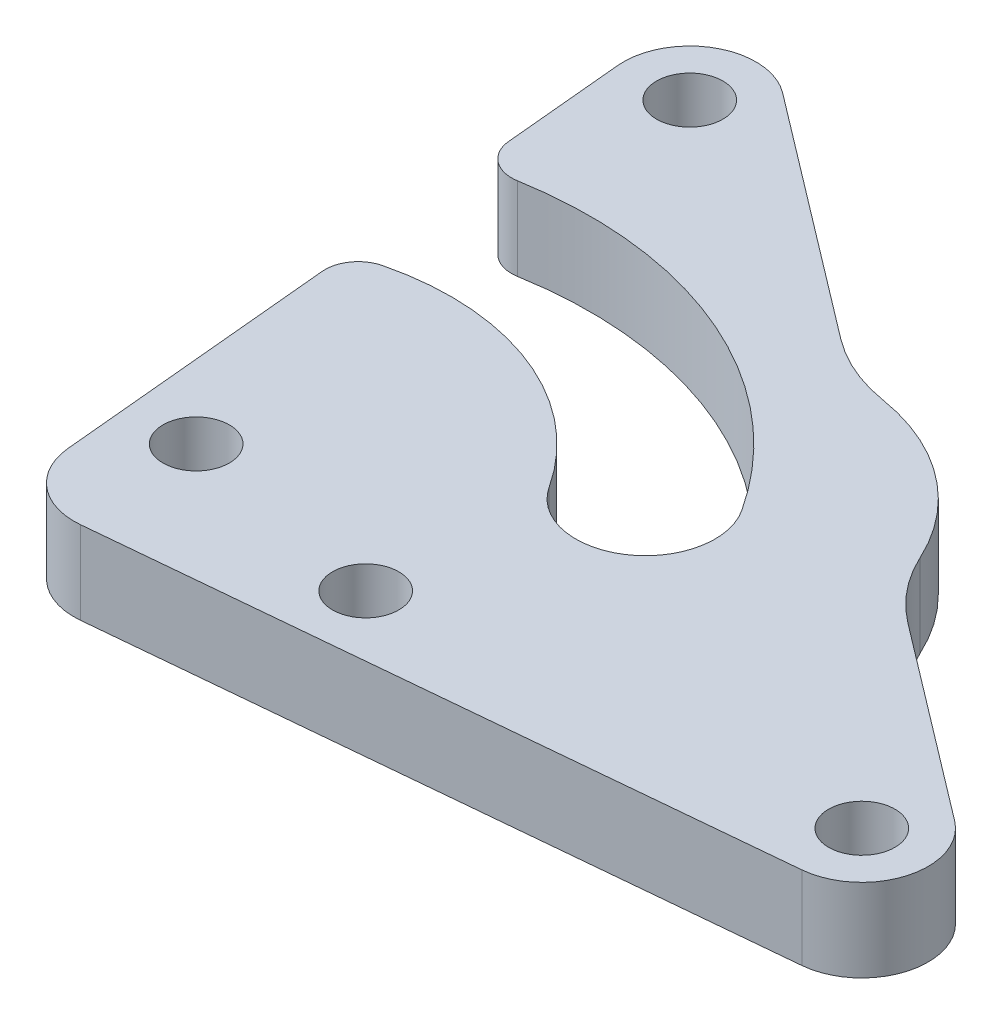
SolidWorks part; units mm, degrees
ref_plane "前视基准面" through (0, 0, 0) normal (0, 0, 1) x (1, 0, 0)
ref_plane "上视基准面" through (0, 0, 0) normal (0, 1, 0) x (1, 0, 0)
ref_plane "右视基准面" through (0, 0, 0) normal (1, 0, 0) x (0, 0, -1)
sketch "草图1" plane through (0, 0, 0) normal (0, 1, 0) x (1, 0, 0)
  line L0 (-20.0875, 0) -> (20.0875, 0) construction
  line L1 (-20.0875, 0) -> (-23.165, 32.8682) construction
  line L2 (-20.0875, 0) -> (-23.165, 32.8682) construction
  line L3 (-23.165, 32.8682) -> (20.0875, 0) construction
  line L4 (-20.0875, 0) -> (-23.165, 32.8682) construction
  line L5 (-24.0701, -0.3729) -> (-27.1475, 32.4954)
  line L6 (-16.1049, 0.3729) -> (-19.1824, 33.2411)
  line L7 (-23.165, 32.8682) -> (20.0875, 0) construction
  line L8 (-20.7448, 36.053) -> (22.5077, 3.1848)
  line L9 (-25.5851, 29.6835) -> (17.6673, -3.1848)
  line L10 (-20.0875, 0) -> (20.0875, 0) construction
  line L11 (-20.0875, 4) -> (20.0875, 4)
  line L12 (-20.0875, -4) -> (20.0875, -4)
  arc A0 (-24.0701, -0.3729) -> (-16.1049, 0.3729) centre (-20.0875, 0) ccw
  arc A1 (-19.1824, 33.2411) -> (-27.1475, 32.4954) centre (-23.165, 32.8682) ccw
  arc A2 (-20.7448, 36.053) -> (-25.5851, 29.6835) centre (-23.165, 32.8682) ccw
  arc A3 (17.6673, -3.1848) -> (22.5077, 3.1848) centre (20.0875, 0) ccw
  arc A4 (-20.0875, 4) -> (-20.0875, -4) centre (-20.0875, 0) ccw
  arc A5 (20.0875, -4) -> (20.0875, 4) centre (20.0875, 0) ccw
  circle A6 centre (-20.0875, 0) radius 2
  circle A7 centre (-23.165, 32.8682) radius 2
  circle A8 centre (20.0875, 0) radius 2
  point P4 (0, 0)
  point P7 (-21.6262, 16.4341)
  point P12 (-1.5387, 16.4341)
  point P18 (0, 0)
  dimension "D4" = 4
  dimension "D5" = 4
  dimension "D6" = 4
  dimension "D7" = 4
  dimension "D8" = 4
  dimension "D1" = 40.175
  dimension "D2" = 33.012
  dimension "D3" = 54.324
extrude "凸台-拉伸1" add sketch "草图1" along normal blind 5 contours L11 A4 A0 L6 A6 | A4 L11 L6 L9 A2 L5 | A1 A2 L9 L6 A7 | A5 L8 A1 L6 L9 L11 | A3 L9 L11 L6 A0 L12 | A3 A5 L11 L9 A8 | L6 L11 L9
sketch "草图2" plane through (0, 5, 0) normal (0, 1, 0) x (1, 0, 0)
  line L0 (-23.165, 32.8682) -> (-20.0875, 0) construction
  line L1 (-20.0875, 0) -> (-19.7384, -3.7287) construction
  line L2 (-19.7384, -3.7287) -> (20.0875, 0) construction
  line L3 (-20.1113, 0.2539) -> (19.7146, 3.9826)
  line L4 (-19.3655, -7.7113) -> (20.4604, -3.9826)
  line L5 (-23.721, -4.1016) -> (-24.0701, -0.3729)
  line L6 (-24.0701, -0.3729) -> (-27.1475, 32.4954) construction
  arc A5 (-20.1113, 0.2539) -> (-19.3655, -7.7113) centre (-19.7384, -3.7287) ccw
  arc A6 (20.4604, -3.9826) -> (19.7146, 3.9826) centre (20.0875, 0) ccw
  arc A7 (-24.0701, -0.3729) -> (-20.0875, -4) centre (-20.0875, 0) ccw construction
  point P4 (0.1746, -1.8643)
  dimension "D2" = 4
  dimension "D1" = 3.745
extrude "凸台-拉伸2" add sketch "草图2" against normal blind 5
sketch "草图3" plane through (0, 5, 0) normal (0, 1, 0) x (1, 0, 0)
  circle A0 centre (-20.0875, 0) radius 19.6
  arc A1 (-33.4302, 14.3573) -> (-3.6558, 10.6846) centre (-20.0875, 0) cw construction
  arc A2 (-0.1348, 12.9742) -> (-36.2893, 17.4339) centre (-20.0875, 0) ccw
  arc A3 (-7.1769, 8.395) -> (-30.571, 11.2808) centre (-20.0875, 0) ccw
  arc A4 (-7.1769, 8.395) -> (-0.1348, 12.9742) centre (-3.6558, 10.6846) ccw
  arc A5 (-36.2893, 17.4339) -> (-30.571, 11.2808) centre (-33.4302, 14.3573) ccw
  point P5 (-17.688, 19.4526)
  line M3 (-27.1475, 32.4954) -> (-23.721, -4.1016)
  dimension "D1" = 39.2
  dimension "D2" = 4.2
  dimension "D3" = 30
extrude "切除-拉伸1" cut sketch "草图3" against normal through all contours A2 A5 A0 M3 | A0 A4 A2 M3 | A3 A4 A0 M3 | A0 A5 A3 M3
sketch "草图4" plane through (0, 5, 0) normal (0, 1, 0) x (1, 0, 0)
  circle A0 centre (-3.6558, 10.6846) radius 12.5
  line M11 (22.5077, 3.1848) -> (-20.7448, 36.053)
  dimension "D1" = 25
extrude "凸台-拉伸3" add sketch "草图4" against normal blind 5 contours A0 M11
fillet "圆角1" radius 10 2 edges at (8.4277, 2.5, -13.8844) (-3.8096, 2.5, -23.1837)
fillet "圆角2" radius 2 2 edges at (-26.2572, 2.5, -22.9864) (-25.4564, 2.5, -14.4338)
sketch "草图5" [suppressed] plane through (0, 0, 0) normal (0, -1, 0) x (1, 0, 0)
  line L0 (-19.3655, 7.7113) -> (-13.3916, 7.152)
  line L1 (-19.3655, 7.7113) -> (20.4604, 3.9826) construction
  line L2 (-13.3916, 7.152) -> (-12.9256, 12.1302)
  line L3 (-12.9256, 12.1302) -> (-18.8994, 12.6895)
  line L4 (-18.8994, 12.6895) -> (-19.3655, 7.7113)
  line L5 (20.4604, 3.9826) -> (14.4865, 4.5419)
  line L6 (14.4865, 4.5419) -> (14.9526, 9.5201)
  line L7 (14.9526, 9.5201) -> (20.9265, 8.9608)
  line L8 (20.9265, 8.9608) -> (20.4604, 3.9826)
  dimension "D1" = 5
  dimension "D2" = 6
  dimension "D3" = 5
  dimension "D4" = 6
sketch "草图6" plane through (0, 5, 0) normal (0, 1, 0) x (1, 0, 0)
  line L0 (-19.3655, -7.7113) -> (20.4604, -3.9826) construction
  line L1 (-23.721, -4.1016) -> (-25.3053, 12.8193) construction
  circle A0 centre (-7.2928, -2.5635) radius 2
  dimension "D1" = 4
  dimension "D2" = 16.5
  dimension "D3" = 4
extrude "切除-拉伸2" cut sketch "草图6" against normal through all
